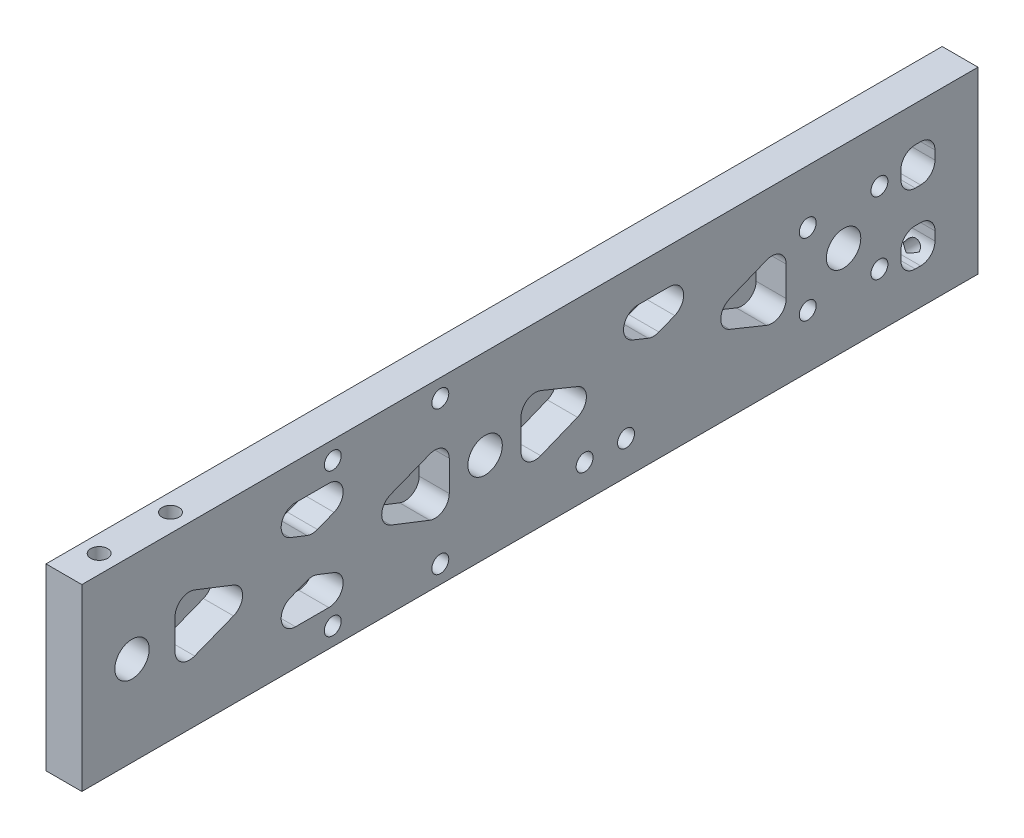
SolidWorks part; units mm, degrees
ref_plane "Front Plane" through (0, 0, 0) normal (0, 0, 1) x (1, 0, 0)
ref_plane "Top Plane" through (0, 0, 0) normal (0, 1, 0) x (1, 0, 0)
ref_plane "Right Plane" through (0, 0, 0) normal (1, 0, 0) x (0, 0, -1)
sketch "Sketch1" plane through (0, 0, 0) normal (0, 1, 0) x (1, 0, 0)
  line L1 (0, 0) -> (-6.35, 0)
  line L2 (0, 0) -> (0, -158.75)
  line L3 (0, -158.75) -> (-6.35, -158.75)
  line L4 (-6.35, 0) -> (-6.35, -158.75)
  dimension "D1" = 158.75
  dimension "D2" = 6.35
extrude "Boss-Extrude1" add sketch "Sketch1" along normal blind 31.75 contours L4 L3 L2 L1
sketch "Sketch2" plane through (0, 0, 0) normal (1, 0, 0) x (0, 0, -1)
  line L0 (6.35, 0) -> (6.35, 38.6089) construction
  line L1 (6.35, 15.875) -> (-159.7103, 15.875) construction
  circle A0 centre (-23.8125, 15.875) radius 3.048
  circle A1 centre (-87.3125, 15.875) radius 3.048
  circle A2 centre (-149.86, 15.875) radius 3.048
  dimension "D3" = 6.096
  dimension "D1" = 6.35
  dimension "D2" = 15.875
  dimension "D4" = 30.1625
  dimension "D5" = 63.5
  dimension "D6" = 156.21
extrude "axle holes" cut sketch "Sketch2" against normal through all
sketch "midwall bolt placement" plane through (0, 0, 0) normal (1, 0, 0) x (0, 0, -1)
  line L0 (-114.3, 3.175) -> (-95.25, 3.175) construction
  line L2 (-158.75, 31.75) -> (-158.75, 0) construction
  circle A0 centre (-114.3, 3.175) radius 1.5875 construction
  circle A1 centre (-95.25, 3.175) radius 1.5875 construction
  dimension "D2" = 19.05
  dimension "D3" = 3.175
  dimension "D1" = 44.45
hole_wizard "Ø3.0mm Dowel Hole2" positions "Sketch5" profile "Sketch6" hole size "Ø3.0" standard "ANSI Metric" end condition through all
sketch "Sketch5" plane through (0, 0, 0) normal (1, 0, 0) x (0, 0, -1)
  point P0 (-114.3, 3.175)
  point P3 (-95.25, 3.175)
sketch "Sketch6" plane through (0, 3.175, 114.3) normal (0, 1, 0) x (0, 0, -1)
  line L0 (0, 0) -> (0, 6.35)
  line L1 (0, 6.35) -> (1.5, 6.35)
  line L2 (1.5, 6.35) -> (1.5, 0)
  line L5 (1.5, 0) -> (0, 0)
  line L11 (0, -6.35) -> (0, 107.95) construction
  dimension "Thru Hole Dia." = 3
  dimension "Thru Hole Depth" = 6.35
sketch "Sketch4" plane through (0, 0, 0) normal (1, 0, 0) x (0, 0, -1)
  line L0 (0, 31.75) -> (-158.75, 31.75) construction
  line L1 (-142.24, 25.4) -> (-93.6625, 25.4)
  line L2 (-142.24, 25.4) -> (-142.24, 6.35)
  line L3 (-142.24, 6.35) -> (-93.6625, 6.35)
  line L4 (-93.6625, 25.4) -> (-93.6625, 6.35)
  line L10 (-80.9625, 25.4) -> (-33.9725, 25.4)
  line L11 (-80.9625, 25.4) -> (-80.9625, 6.35)
  line L19 (-80.9625, 6.35) -> (-33.9725, 6.35)
  line L23 (-33.9725, 25.4) -> (-33.9725, 6.35)
  line L28 (-13.6525, 25.4) -> (-7.62, 25.4)
  line L29 (-13.6525, 25.4) -> (-13.6525, 6.35)
  line L30 (-13.6525, 6.35) -> (-7.62, 6.35)
  line L31 (-7.62, 25.4) -> (-7.62, 6.35)
  line L32 (0, 0) -> (-158.75, 0) construction
  line L33 (-13.6525, 15.875) -> (-7.62, 15.875) construction
  line L34 (-33.9725, 25.4) -> (-80.9625, 6.35) construction
  line L35 (-80.9625, 25.4) -> (-33.9725, 6.35) construction
  line L40 (-93.6625, 25.4) -> (-142.24, 6.35) construction
  line L41 (-142.24, 25.4) -> (-93.6625, 6.35) construction
  line L42 (-143.2938, 22.7129) -> (-94.7163, 3.6629)
  line L43 (-94.7163, 28.0871) -> (-143.2938, 9.0371)
  line L44 (-35.0569, 28.0749) -> (-82.0469, 9.0249)
  line L45 (-82.0469, 22.7251) -> (-35.0569, 3.6751)
  line L46 (-13.6525, 12.9886) -> (-7.62, 12.9886)
  line L47 (-141.1862, 28.0871) -> (-92.6087, 9.0371)
  line L48 (-92.6087, 22.7129) -> (-141.1862, 3.6629)
  line L49 (-32.8881, 22.7251) -> (-79.8781, 3.6751)
  line L50 (-79.8781, 28.0749) -> (-32.8881, 9.0249)
  line L51 (-13.6525, 18.7614) -> (-7.62, 18.7614)
  circle A1 centre (-23.8125, 15.875) radius 3.048 construction
  circle A16 centre (-87.3125, 15.875) radius 3.048 construction
  circle A17 centre (-149.86, 15.875) radius 3.048 construction
  dimension "D2" = 6.35
  dimension "D1" = 6.35
  dimension "D3" = 10.16
  dimension "D4" = 10.16
  dimension "D5" = 6.35
  dimension "D6" = 6.35
  dimension "D7" = 7.62
  dimension "D8" = 7.62
  dimension "D9" = 2.8864
  dimension "D10" = 2.8864
extrude "cheesing cut" cut sketch "Sketch4" against normal blind 5.334 contours L43 L42 L2 | L1 L47 L43 | L4 L48 L47 | L42 L48 L3 | L45 L11 L44 | L10 L50 L44 | L49 L50 L23 | L46 L29 L30 L31 | L29 L51 L31 L28
fillet "Fillet1" radius 2.54 29 edges at (-2.667, 15.875, 65.15) (-2.667, 6.35, 13.6525) (-2.667, 12.9886, 13.6525) (-2.667, 12.9886, 7.62) (-2.667, 6.35, 7.62) (-2.667, 18.7614, 7.62) (-2.667, 25.4, 7.62) (-2.667, 25.4, 13.6525) (-2.667, 18.7614, 13.6525) (-2.667, 15.875, 49.785) (-2.667, 9.4645, 33.9725) (-2.667, 22.2855, 33.9725) (-2.667, 25.4, 41.655) (-2.667, 25.4, 73.28) (-2.667, 18.9895, 57.4675) (-2.667, 9.4645, 80.9625) (-2.667, 22.2855, 80.9625) (-2.667, 6.35, 101.5684) (-2.667, 25.4, 101.5684) (-2.667, 15.875, 125.8572) (-2.667, 9.4504, 142.24) (-2.667, 22.2996, 142.24) (-2.667, 25.4, 134.3341) (-2.667, 6.35, 134.3341) (-2.667, 12.7746, 117.9512) (-2.667, 18.9754, 117.9512) (-2.667, 15.875, 110.0453) (-2.667, 22.2996, 93.6625) (-2.667, 9.4504, 93.6625)
ref_plane "Plane1" through (0, 15.875, 0) normal (0, 1, 0) x (1, 0, 0)
mirror "Mirror1" about plane through (0, 15.875, 0) normal (0, 1, 0) of "Ø3.0mm Dowel Hole2"
sketch "Sketch11" plane through (0, 0, 0) normal (1, 0, 0) x (0, 0, -1)
sketch "Sketch12" plane through (0, 0, 0) normal (1, 0, 0) x (0, 0, -1)
  line L0 (-69.6854, 6) -> (-62.3514, 6) construction
  line L1 (0, 0) -> (-158.75, 0) construction
  dimension "D1" = 6
hole_wizard "Ø3.0mm Dowel Hole1" positions "Sketch13" profile "Sketch14" hole size "Ø3.0" standard "ANSI Metric" end condition through all
sketch "Sketch13" plane through (0, 0, 0) normal (1, 0, 0) x (0, 0, -1)
  point P0 (-69.6854, 6)
  point P3 (-62.3514, 6)
sketch "Sketch14" plane through (0, 6, 69.6854) normal (0, 1, 0) x (0, 0, -1)
  line L0 (0, 0) -> (0, 6.35)
  line L1 (0, 6.35) -> (1.5, 6.35)
  line L2 (1.5, 6.35) -> (1.5, 0)
  line L5 (1.5, 0) -> (0, 0)
  line L11 (0, -6.35) -> (0, 107.95) construction
  dimension "Thru Hole Dia." = 3
  dimension "Thru Hole Depth" = 6.35
hole_wizard "M3x0.5 Tapped Hole3" positions "Sketch15" profile "Sketch16" hole size "Ø3.0" standard "ANSI Metric"
sketch "Sketch15" plane through (101.3428, 5.2515, -6.35) normal (0, 0, -1) x (-1, 0, 0)
  point P0 (104.5178, 20.1485)
  point P3 (104.5178, 1.0985)
sketch "Sketch16" plane through (-3.175, 25.4, -6.35) normal (1, 0, 0) x (0, 1, 0)
  line L0 (0, 0) -> (0, 15.9013)
  line L1 (0, 15.9013) -> (1.5, 15)
  line L2 (1.5, 15) -> (1.5, 0)
  line L5 (1.5, 0) -> (0, 0)
  line L10 (0, 15.9013) -> (-1.5, 15) construction
  line L11 (0, -6.35) -> (0, 107.95) construction
  dimension "Hole Dia." = 3
  dimension "Hole Depth" = 15
  dimension "Drill Angle" = 118
hole_wizard "" positions "Sketch17" profile "Sketch18" hole size "Ø3.0" standard "ANSI Metric"
sketch "Sketch17" plane through (-6.35, -2.87, -6.3443) normal (0, -1, 0.002) x (-1, 0, 0)
  point P0 (-3.1133, -146.1573)
  point P2 (-3.1133, -158.7939)
sketch "Sketch18" plane through (-3.2367, -2.5779, 139.8127) normal (1, 0, 0) x (0, -0.002, -1)
  line L0 (0, 0) -> (0, 8.5213)
  line L1 (0, 8.5213) -> (1.5, 7.62)
  line L2 (1.5, 7.62) -> (1.5, 0)
  line L3 (1.5, 0) -> (0, 0)
  line L4 (0, 8.5213) -> (-1.5, 7.62) construction
  line L5 (0, -6.35) -> (0, 107.95) construction
  dimension "Hole Dia." = 3
  dimension "Hole Depth" = 7.62
  dimension "Drill Angle" = 118
mirror "Mirror2" about plane through (0, 15.875, 0) normal (0, 1, 0) of ""
sketch "Sketch19" plane through (0, 0, 0) normal (1, 0, 0) x (0, 0, -1)
  line L0 (-23.8125, 15.875) -> (-30.1625, 22.225) construction
  line L1 (-23.8125, 15.875) -> (-30.0381, 15.875) construction
  line L2 (-23.8125, 15.875) -> (-30.1625, 9.525) construction
  line L3 (-30.1625, 9.525) -> (-30.1625, 22.225) construction
  circle A0 centre (-23.8125, 15.875) radius 3.048 construction
  circle A1 centre (-23.8125, 15.875) radius 3.048 construction
  circle A2 centre (-30.1625, 22.225) radius 1.9087 construction
  dimension "D1" = 45
  dimension "D2" = 12.7
hole_wizard "Ø3.0mm Dowel Hole4" positions "Sketch20" profile "Sketch21" hole size "Ø3.0" standard "ANSI Metric" end condition through all
sketch "Sketch20" plane through (0, 0, 0) normal (1, 0, 0) x (0, 0, -1)
  point P0 (-30.1625, 22.225)
sketch "Sketch21" plane through (0, 22.225, 30.1625) normal (0, 1, 0) x (0, 0, -1)
  line L0 (0, 0) -> (0, 6.35)
  line L1 (0, 6.35) -> (1.5, 6.35)
  line L2 (1.5, 6.35) -> (1.5, 0)
  line L5 (1.5, 0) -> (0, 0)
  line L11 (0, -6.35) -> (0, 107.95) construction
  dimension "Thru Hole Dia." = 3
  dimension "Thru Hole Depth" = 6.35
pattern_circular "CirPattern1" count 4 over 360 about axis through (0, 15.875, 23.8125) along (1, 0, 0) of "Ø3.0mm Dowel Hole4"
equation "\"width\" = 6in 'side to side 6"
equation "\"height\"= 1.25in'top to bottom from 1.25"
equation "\"length\"=6.25in 'back to front 6.25"
equation "\"side_width\"= 1in"
equation "\"wheel_di\"=1.875in'2.375"
equation "\"wepon_di\" = 1.25in ' milled rectangle must compensate for bolts ~ - .5 1.5"
equation "\"wepon_axle\" = 0.1in ' placement from front .5"
equation "\"frame_bolts\" = 0.125"
equation "\"D1@Sketch1\"=\"length\""
equation "\"D1@Boss-Extrude1\"=\"height\""
equation "\"D2@Sketch2\"=\"height\"/2"
equation "\"D4@Sketch2\"=\"wheel_di\"/2+.25"
equation "\"D6@Sketch2\"=\"length\" - .1"
equation "\"D2@midwall bolt placement\" = \"height\" - .5"
equation "\"wheel_base\"= 2.5in"
equation "\"D5@Sketch2\"=\"wheel_base\""
equation "\"cheesing\" = .25in ' width of general trusses"
equation "\"D1@Sketch4\"=\"cheesing\""
equation "\"D2@Sketch4\"=\"cheesing\""
equation "\"D9@Sketch4\"=\"D10@Sketch4\""
equation "\"D10@Sketch4\"=\"cheesing\"/2.2"
equation "\"D1@midwall bolt placement\"=\"wepon_di\"+.5"
